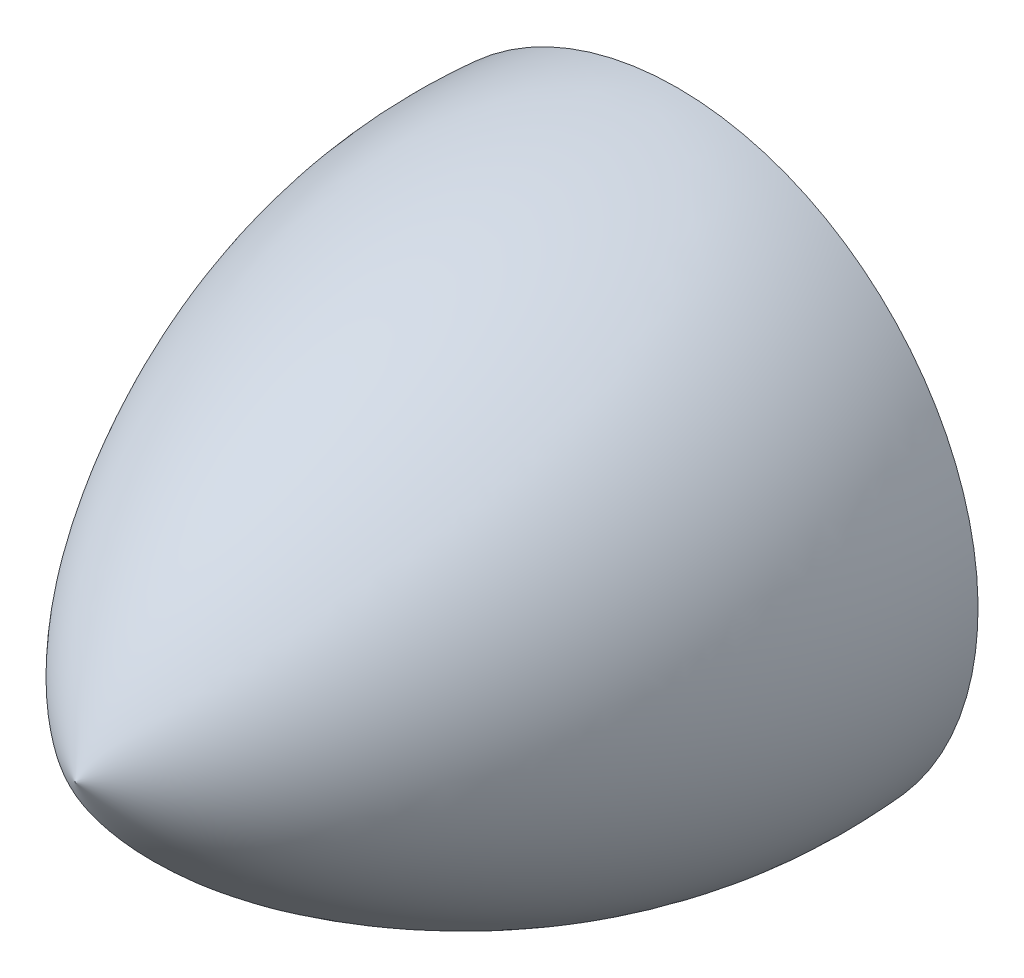
SolidWorks part; units mm, degrees
ref_plane "Front Plane" through (0, 0, 0) normal (0, 0, 1) x (1, 0, 0)
ref_plane "Top Plane" through (0, 0, 0) normal (0, 1, 0) x (1, 0, 0)
ref_plane "Right Plane" through (0, 0, 0) normal (1, 0, 0) x (0, 0, -1)
sketch "Sketch1" plane through (0, 0, 0) normal (1, 0, 0) x (0, 0, -1)
  line L0 (0, -35) -> (0, 35)
  line L1 (0, 0) -> (-70.104, 0) construction
  line L2 (0, -35) -> (-70.104, 0)
  spline S0 degree 3 poles (-70.104, 0) (-64.6188, 11.1696) (-42.348, 28.8049) (-15.522, 36.223) (0, 35) knots 0 0 0 0 0.44611 1 1 1 1
  point P3 (-62.8884, 10.5387)
  point P4 (0, 0)
  point P7 (-43.8418, 24.8708)
  point P8 (-25.361, 32.414)
  dimension "D1" = 70
  dimension "D2" = 70.104
revolve "Revolve1" add sketch "Sketch1" angle 360 about L1
